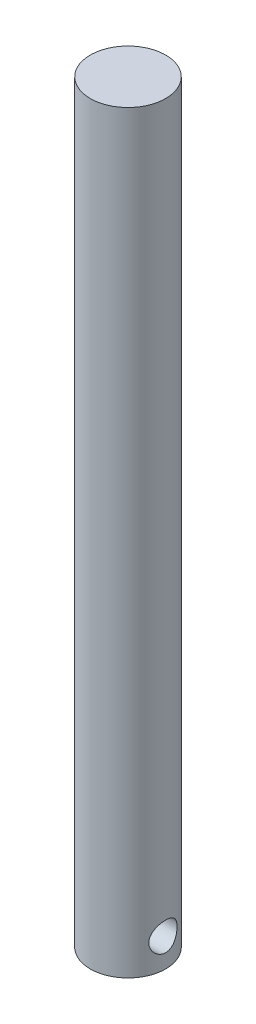
SolidWorks part; units mm, degrees
ref_plane "Front Plane" through (0, 0, 0) normal (0, 0, 1) x (1, 0, 0)
ref_plane "Top Plane" through (0, 0, 0) normal (0, 1, 0) x (1, 0, 0)
ref_plane "Right Plane" through (0, 0, 0) normal (1, 0, 0) x (0, 0, -1)
sketch "Sketch1" plane through (0, 0, 0) normal (0, 1, 0) x (1, 0, 0)
  circle A0 centre (0, 0) radius 20
  dimension "D1" = 40
extrude "Boss-Extrude1" add sketch "Sketch1" along normal blind 400
sketch "Sketch2" plane through (0, 0, 0) normal (1, 0, 0) x (0, 0, -1)
  line L0 (-20, 0) -> (20, 0) construction
  circle A0 centre (0, 15) radius 7.5
  dimension "D1" = 15
  dimension "D2" = 15
extrude "Cut-Extrude1" cut sketch "Sketch2" against normal through all both and the other way through all
